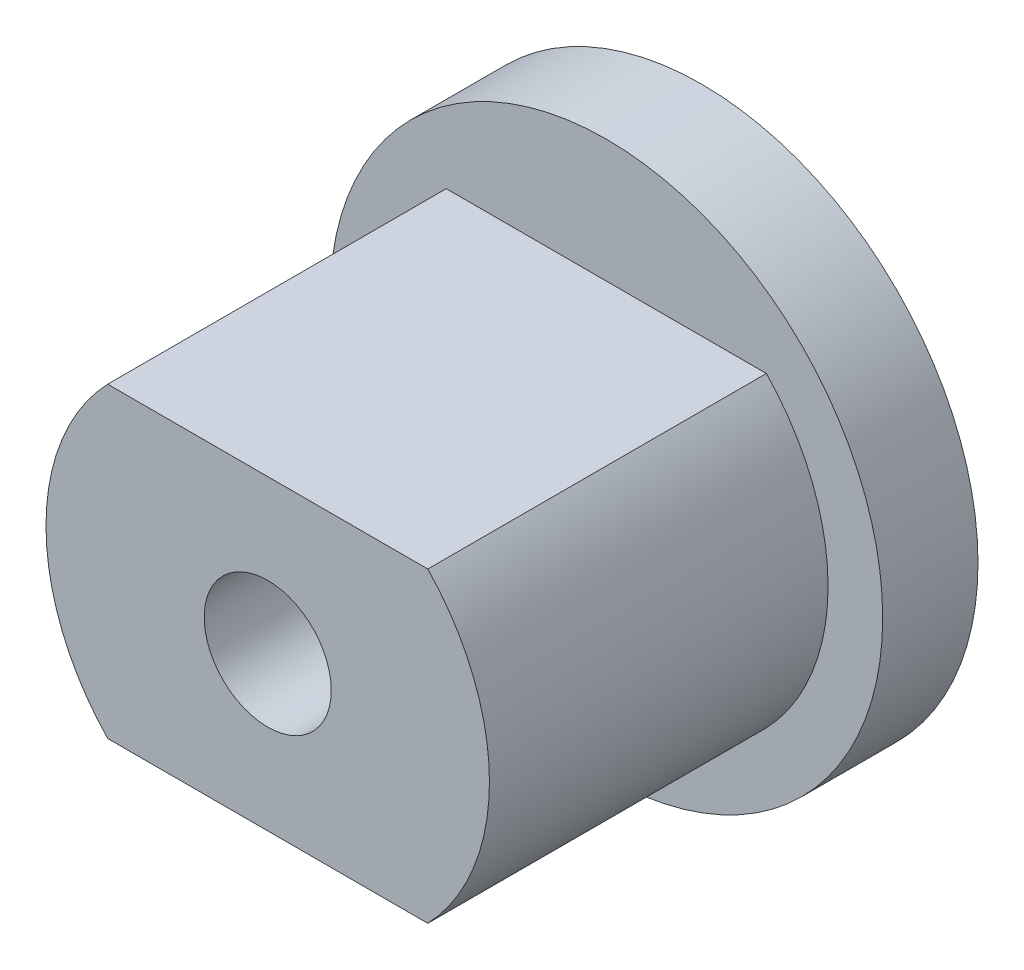
SolidWorks part; units mm, degrees
material "Nylon 101"
ref_plane "Plan de face" through (0, 0, 0) normal (0, 0, 1) x (1, 0, 0)
ref_plane "Plan de dessus" through (0, 0, 0) normal (0, 1, 0) x (1, 0, 0)
ref_plane "Plan de droite" through (0, 0, 0) normal (1, 0, 0) x (0, 0, -1)
sketch "Esquisse1" plane through (0, 0, 0) normal (0, 0, 1) x (1, 0, 0)
  line L0 (-6.8541, 0) -> (6.814, 0) construction
  line L1 (-2.5195, 2.415) -> (2.5195, 2.415)
  line L2 (-2.5195, -2.415) -> (2.5195, -2.415)
  arc A0 (-2.5195, 2.415) -> (-2.5195, -2.415) centre (0, 0) ccw
  arc A1 (2.5195, -2.415) -> (2.5195, 2.415) centre (0, 0) ccw
  dimension "D1" = 6.98
  dimension "D2" = 4.83
extrude "Boss.-Extru.1" add sketch "Esquisse1" along normal blind 5.33
sketch "Esquisse2" plane through (0, 0, 5.33) normal (0, 0, 1) x (1, 0, 0)
  circle A0 centre (0, 0) radius 1
  dimension "D1" = 2
extrude "Enlèv. mat.-Extru.1" cut sketch "Esquisse2" against normal blind 3
sketch "Esquisse3" plane through (0, 0, 0) normal (0, 0, -1) x (-1, 0, 0)
  circle A0 centre (0, 0) radius 4.35
  dimension "D1" = 8.7
extrude "Boss.-Extru.2" add sketch "Esquisse3" along normal blind 1.5
